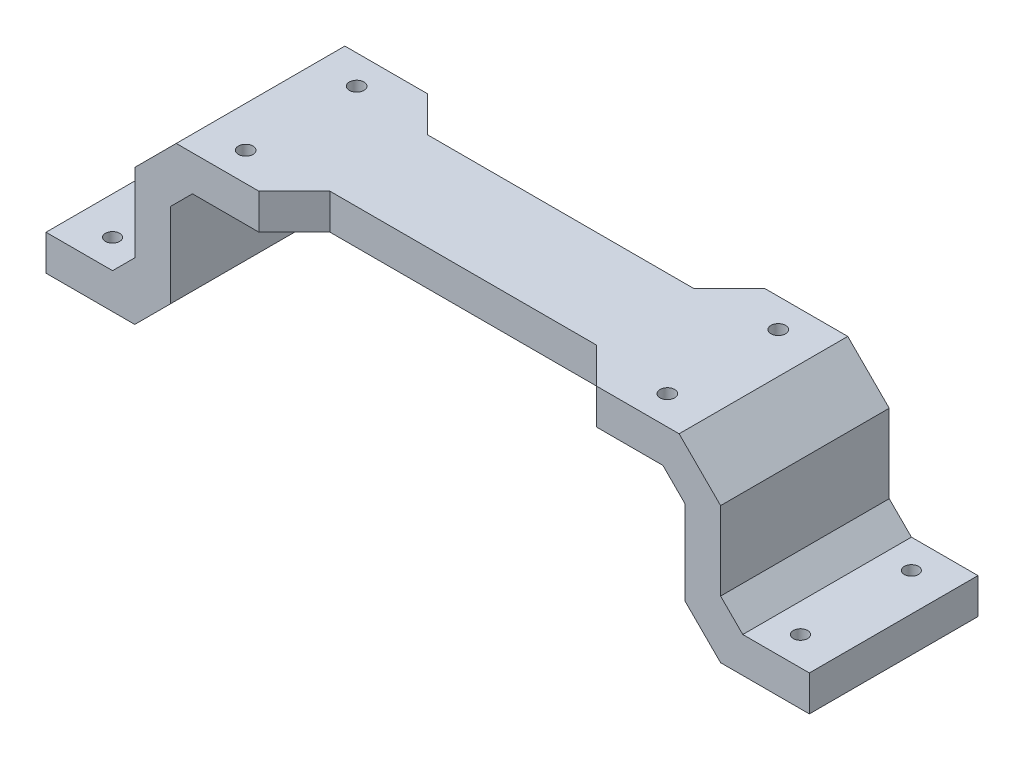
SolidWorks part; units mm, degrees
ref_plane "Front Plane" through (0, 0, 0) normal (0, 0, 1) x (1, 0, 0)
ref_plane "Top Plane" through (0, 0, 0) normal (0, 1, 0) x (1, 0, 0)
ref_plane "Right Plane" through (0, 0, 0) normal (1, 0, 0) x (0, 0, -1)
sketch "Sketch1" plane through (0, 0, 0) normal (0, 0, 1) x (1, 0, 0)
  line L0 (47.5, -43) -> (47.5, -8) construction
  line L1 (-240, -43) -> (335, -43) construction
  line L2 (-90, -40) -> (185, -40) construction
  line L3 (-38.5, -40) -> (-18.5, -40)
  line L4 (-38.5, -40) -> (-38.5, -32)
  line L5 (-38.5, -32) -> (-23.5, -32)
  line L9 (-10.5, -32) -> (-10.5, -13)
  line L11 (-18.5, -27) -> (-18.5, -9.3442)
  line L12 (-5.5, -8) -> (100.5, -8)
  line L14 (-9.1558, 0) -> (104.1558, 0)
  line L16 (-23.5, -32) -> (-18.5, -27)
  line L17 (-10.5, -13) -> (-5.5, -8)
  line L18 (-18.5, -9.3442) -> (-9.1558, 0)
  line L19 (-18.5, -40) -> (-10.5, -32)
  line L20 (47.5, -2.5301) -> (47.5, 2.8418) construction
  line L21 (113.5, -40) -> (105.5, -32)
  line L22 (113.5, -9.3442) -> (104.1558, 0)
  line L23 (105.5, -13) -> (100.5, -8)
  line L24 (118.5, -32) -> (113.5, -27)
  line L25 (113.5, -27) -> (113.5, -9.3442)
  line L26 (105.5, -32) -> (105.5, -13)
  line L27 (133.5, -32) -> (118.5, -32)
  line L28 (133.5, -40) -> (133.5, -32)
  line L29 (133.5, -40) -> (113.5, -40)
  line L30 (-7.5, 0) -> (7.5, 0) construction
  point P7 (-10.5, -40)
  point P10 (-12.5, -39.6496)
  point P11 (-10.5, -8)
  point P12 (-18.5, -32)
  point P14 (-17.0172, -1.4828)
  point P22 (0, 0)
  point P23 (-17.5, -2.3042)
  point P25 (0, 0)
  point P38 (112.0172, -1.4828)
  point P39 (113.5, -32)
  point P40 (105.5, -8)
  point P41 (105.5, -40)
  dimension "D1" = 8
  dimension "D2" = 8
  dimension "D3" = 8
  dimension "D5" = 20
extrude "Extrude1" add sketch "Sketch1" against normal blind 46
sketch "Sketch2" plane through (0, -40, 0) normal (0, -1, 0) x (1, 0, 0)
  circle A0 centre (-30, -14.5) radius 1.6 construction
  circle A1 centre (-30, -39.5) radius 1.6 construction
  circle A2 centre (125, -14.5) radius 1.6 construction
  circle A3 centre (125, -39.5) radius 1.6 construction
  circle A4 centre (-30, -14.5) radius 1.6
  circle A5 centre (-30, -39.5) radius 1.6
  circle A6 centre (125, -14.5) radius 1.6
  circle A7 centre (125, -39.5) radius 1.6
  arc A8 (0, -16.15) -> (0, -12.85) centre (0, -14.5) ccw construction
  arc A9 (0, -12.85) -> (0, -16.15) centre (0, -14.5) ccw construction
  arc A10 (0, -41.15) -> (0, -37.85) centre (0, -39.5) ccw construction
  arc A11 (0, -37.85) -> (0, -41.15) centre (0, -39.5) ccw construction
  arc A12 (95, -16.15) -> (95, -12.85) centre (95, -14.5) ccw construction
  arc A13 (95, -41.15) -> (95, -37.85) centre (95, -39.5) ccw construction
  arc A14 (95, -12.85) -> (95, -16.15) centre (95, -14.5) ccw construction
  arc A15 (95, -37.85) -> (95, -41.15) centre (95, -39.5) ccw construction
  arc A16 (0, -16.15) -> (0, -12.85) centre (0, -14.5) ccw
  arc A17 (0, -12.85) -> (0, -16.15) centre (0, -14.5) ccw
  arc A18 (0, -41.15) -> (0, -37.85) centre (0, -39.5) ccw
  arc A19 (0, -37.85) -> (0, -41.15) centre (0, -39.5) ccw
  arc A20 (95, -16.15) -> (95, -12.85) centre (95, -14.5) ccw
  arc A21 (95, -41.15) -> (95, -37.85) centre (95, -39.5) ccw
  arc A22 (95, -12.85) -> (95, -16.15) centre (95, -14.5) ccw
  arc A23 (95, -37.85) -> (95, -41.15) centre (95, -39.5) ccw
extrude "Cut-Extrude1" cut sketch "Sketch2" against normal blind 5000
sketch "Sketch3" plane through (0, 0, 0) normal (0, 0, 1) x (1, 0, 0)
  line L20 (-38.5, -32) -> (-38.5, -40)
  line L21 (-38.5, -40) -> (-18.5, -40)
  line L22 (-18.5, -40) -> (-10.5, -32)
  line L23 (-10.5, -32) -> (-10.5, -13)
  line L24 (-10.5, -13) -> (-5.5, -8)
  line L25 (-5.5, -8) -> (100.5, -8)
  line L26 (100.5, -8) -> (105.5, -13)
  line L27 (105.5, -13) -> (105.5, -32)
  line L28 (105.5, -32) -> (113.5, -40)
  line L29 (113.5, -40) -> (133.5, -40)
  line L30 (133.5, -40) -> (133.5, -32)
  line L31 (133.5, -32) -> (118.5, -32)
  line L32 (118.5, -32) -> (113.5, -27)
  line L33 (113.5, -27) -> (113.5, -9.3442)
  line L34 (113.5, -9.3442) -> (104.1558, 0)
  line L35 (104.1558, 0) -> (-9.1558, 0)
  line L36 (-9.1558, 0) -> (-18.5, -9.3442)
  line L37 (-18.5, -9.3442) -> (-18.5, -27)
  line L38 (-18.5, -27) -> (-23.5, -32)
  line L39 (-23.5, -32) -> (-38.5, -32)
  line L40 (-38.5, -32) -> (-38.5, -40)
  line L41 (-38.5, -40) -> (-18.5, -40)
  line L42 (-18.5, -40) -> (-10.5, -32)
  line L43 (-10.5, -32) -> (-10.5, -13)
  line L44 (-10.5, -13) -> (-5.5, -8)
  line L45 (-5.5, -8) -> (100.5, -8)
  line L46 (100.5, -8) -> (105.5, -13)
  line L47 (105.5, -13) -> (105.5, -32)
  line L48 (105.5, -32) -> (113.5, -40)
  line L49 (113.5, -40) -> (133.5, -40)
  line L50 (133.5, -40) -> (133.5, -32)
  line L51 (133.5, -32) -> (118.5, -32)
  line L52 (118.5, -32) -> (113.5, -27)
  line L53 (113.5, -27) -> (113.5, -9.3442)
  line L54 (113.5, -9.3442) -> (104.1558, 0)
  line L55 (104.1558, 0) -> (-9.1558, 0)
  line L56 (-9.1558, 0) -> (-18.5, -9.3442)
  line L57 (-18.5, -9.3442) -> (-18.5, -27)
  line L58 (-18.5, -27) -> (-23.5, -32)
  line L59 (-23.5, -32) -> (-38.5, -32)
  dimension "D1" = 0
extrude "Extrude2" cut sketch "Sketch3" against normal blind 8
sketch "Sketch4" plane through (0, 0, 0) normal (0, 1, 0) x (1, 0, 0)
  line L0 (9.5, 46) -> (17.5, 38)
  line L1 (104.1558, 46) -> (-9.1558, 46) construction
  line L2 (17.5, 38) -> (77.5, 38)
  line L3 (77.5, 38) -> (85.5, 46)
  line L4 (85.5, 46) -> (9.5, 46)
  line L5 (-9.1558, 27) -> (104.1558, 27) construction
  line L6 (-9.1558, 46) -> (-9.1558, 8) construction
  line L7 (104.1558, 46) -> (104.1558, 8) construction
  line L8 (85.5, 8) -> (9.5, 8)
  line L9 (77.5, 16) -> (85.5, 8)
  line L10 (17.5, 16) -> (77.5, 16)
  line L11 (9.5, 8) -> (17.5, 16)
  dimension "D1" = 45
  dimension "D2" = 45
  dimension "D3" = 8
  dimension "D4" = 15
  dimension "D5" = 15
extrude "Extrude3" cut sketch "Sketch4" against normal blind 8
